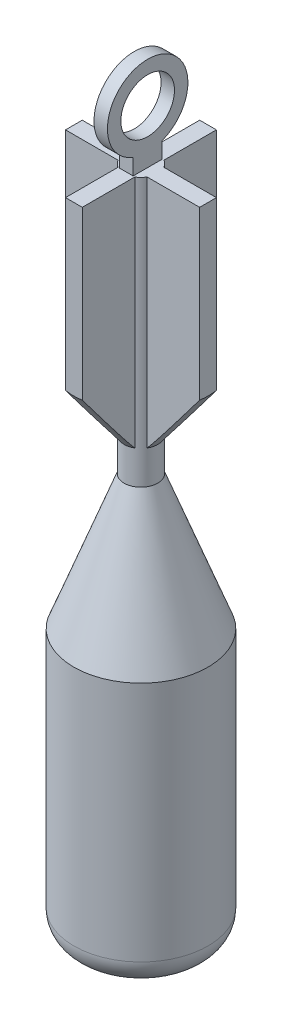
SolidWorks part; units mm, degrees
material "AISI 304"
ref_plane "Front Plane" through (0, 0, 0) normal (0, 0, 1) x (1, 0, 0)
ref_plane "Top Plane" through (0, 0, 0) normal (0, 1, 0) x (1, 0, 0)
ref_plane "Right Plane" through (0, 0, 0) normal (1, 0, 0) x (0, 0, -1)
sketch "Sketch1" plane through (0, 0, 0) normal (0, 1, 0) x (1, 0, 0)
  circle A0 centre (0, 0) radius 6.35
extrude "Extrude1" add sketch "Sketch1" along normal blind 25.4
fillet "Fillet1" radius 2.54 1 edges at (0, 0, 6.35)
sketch "Sketch2" plane through (0, 0, 0) normal (1, 0, 0) x (0, 0, -1)
  line L0 (-6.35, 25.4) -> (0, 25.4)
  line L1 (6.35, 25.4) -> (-6.35, 25.4) construction
  line L2 (0, 25.4) -> (0, 63.5)
  line L3 (-6.35, 25.4) -> (-1.5875, 38.1)
  line L4 (-1.5875, 38.1) -> (-1.5875, 63.5)
  line L5 (-1.5875, 63.5) -> (0, 63.5)
  line L6 (0, 66.5958) -> (0, 25.4) construction
  dimension "D1" = 38.1
  dimension "D2" = 25.4
  dimension "D3" = 1.5875
revolve "Revolve1" add sketch "Sketch2" angle 360 about L6
sketch "Sketch4" plane through (0, 63.5, 0) normal (0, 1, 0) x (-1, 0, 0)
  circle A0 centre (0, 0) radius 6.35
sketch "Sketch3" plane through (0, 63.5, 0) normal (0, 1, 0) x (-1, 0, 0)
  line L0 (0.7937, -0.7937) -> (0.7938, -6.35)
  line L1 (0.7938, -6.35) -> (-0.7937, -6.35)
  line L2 (-0.7937, -6.35) -> (-0.7937, -0.7937)
  line L3 (-0.7937, -0.7937) -> (-6.35, -0.7938)
  line L4 (-6.35, -0.7938) -> (-6.35, 0.7937)
  line L5 (-6.35, 0.7937) -> (-0.7937, 0.7937)
  line L6 (-0.7937, 0.7937) -> (-0.7937, 6.35)
  line L7 (-0.7937, 6.35) -> (0.7938, 6.35)
  line L8 (0.7938, 6.35) -> (0.7937, 0.7937)
  line L9 (0.7937, 0.7937) -> (6.35, 0.7937)
  line L10 (6.35, 0.7937) -> (6.35, -0.7937)
  line L11 (6.35, -0.7937) -> (0.7937, -0.7937)
  dimension "D1" = 0.7937
  dimension "D2" = 1.5875
  dimension "D3" = 1.5875
  dimension "D4" = 0.7937
  dimension "D5" = 6.35
sketch "Sketch5" plane through (0, 0, 0) normal (1, 0, 0) x (0, 0, -1)
  line L0 (0, 0) -> (0, 65.7151) construction
extrude "Extrude2" add sketch "Sketch3" against normal blind 22.225
sketch "Sketch7" plane through (0, 0, 0) normal (1, 0, 0) x (0, 0, -1)
  line L0 (7.4383, 49.0761) -> (1.5875, 41.275)
  line L2 (7.4383, 49.0761) -> (7.4383, 41.275)
  line L3 (7.4383, 41.275) -> (1.5875, 41.275)
  line L4 (0, 0) -> (0, 65.7151) construction
  point P3 (6.35, 47.625)
  dimension "D1" = 6.35
  dimension "D2" = 6.35
revolve "Cut-Revolve5" cut sketch "Sketch7" angle 360 about L0
sketch "Sketch9" plane through (0, 0, 0) normal (1, 0, 0) x (0, 0, -1)
  line L0 (-1.3748, 63.5) -> (-1.3748, 65.024)
  line L1 (-1.3748, 63.5) -> (1.3748, 63.5)
  line L2 (1.3748, 63.5) -> (1.3748, 65.024)
  circle A0 centre (0, 68.5773) radius 2.54
  arc A1 (-1.3748, 65.024) -> (1.3748, 65.024) centre (0, 68.5773) cw
  dimension "D1" = 1.524
extrude "Extrude3" add sketch "Sketch9" along normal blind 0.635 and the other way blind 0.635
